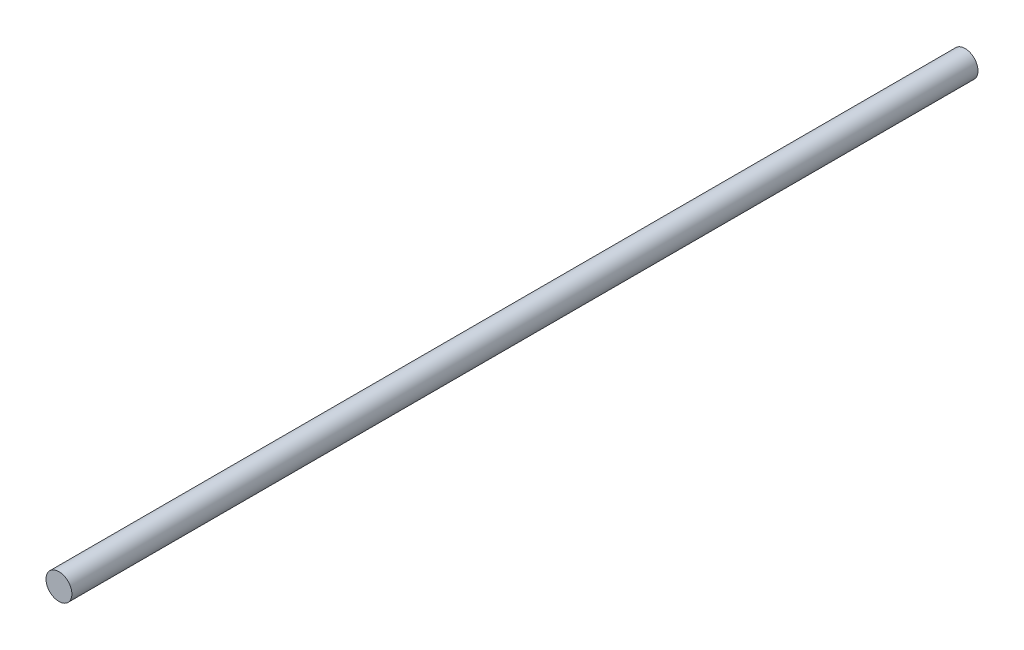
SolidWorks part; units mm, degrees
ref_plane "Front Plane" through (0, 0, 0) normal (0, 0, 1) x (1, 0, 0)
ref_plane "Top Plane" through (0, 0, 0) normal (0, 1, 0) x (1, 0, 0)
ref_plane "Right Plane" through (0, 0, 0) normal (1, 0, 0) x (0, 0, -1)
sketch "Sketch1" plane through (0, 0, 0) normal (0, 0, 1) x (1, 0, 0)
  circle A0 centre (0, 0) radius 1.5
  dimension "D1" = 3
extrude "Boss-Extrude1" add sketch "Sketch1" along normal blind 105
